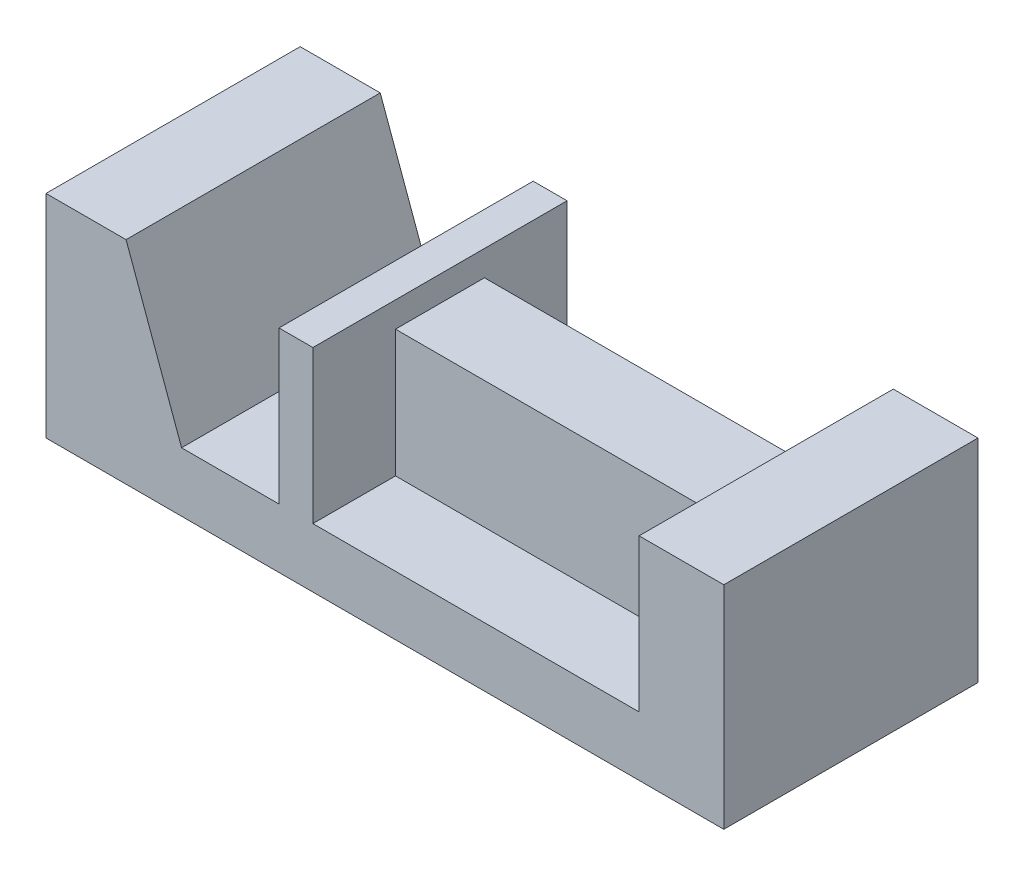
SolidWorks part; units mm, degrees
material "Cast Alloy Steel"
ref_plane "Front Plane" through (0, 0, 0) normal (0, 0, 1) x (1, 0, 0)
ref_plane "Top Plane" through (0, 0, 0) normal (0, 1, 0) x (1, 0, 0)
ref_plane "Right Plane" through (0, 0, 0) normal (1, 0, 0) x (0, 0, -1)
other "Center of Mass"
sketch "Sketch2" plane through (0, 0, 0) normal (0, 0, 1) x (1, 0, 0)
  line L1 (-58.275, 50) -> (101.725, 50)
  line L2 (-58.275, 50) -> (-58.275, 0)
  line L3 (-58.275, 0) -> (101.725, 0)
  line L4 (101.725, 50) -> (101.725, 0)
  dimension "D1" = 160
  dimension "D2" = 50
extrude "Boss-Extrude1" add sketch "Sketch2" along normal blind 60
sketch "Sketch3" plane through (0, 0, 60) normal (0, 0, 1) x (1, 0, 0)
  line L0 (-39.3779, 50) -> (-26.275, 14)
  line L1 (101.725, 50) -> (-58.275, 50) construction
  line L2 (-26.275, 14) -> (-3.275, 14)
  line L3 (-3.275, 14) -> (-3.275, 50)
  line L4 (-3.275, 50) -> (-39.3779, 50)
  line L5 (-39.3779, 50) -> (-39.3779, 0) construction
  line L6 (-58.275, 0) -> (101.725, 0) construction
  dimension "D1" = 23
  dimension "D2" = 20
  dimension "D3" = 14
  dimension "D4" = 55
extrude "Cut-Extrude1" cut sketch "Sketch3" against normal through all
sketch "Sketch4" plane through (0, 0, 60) normal (0, 0, 1) x (1, 0, 0)
  line L0 (4.725, 50) -> (4.725, 14)
  line L1 (101.725, 50) -> (-3.275, 50) construction
  line L2 (4.725, 14) -> (81.725, 14)
  line L3 (81.725, 14) -> (81.725, 50)
  line L4 (81.725, 50) -> (4.725, 50)
  line L5 (-58.275, 0) -> (101.725, 0) construction
  dimension "D1" = 77
  dimension "D2" = 140
  dimension "D3" = 14
extrude "Cut-Extrude3" cut sketch "Sketch4" against normal through all
sketch "Sketch9" plane through (0, 14, 0) normal (0, 1, 0) x (1, 0, 0)
  line L0 (81.725, -30) -> (4.725, -30) construction
  line L1 (81.725, 0) -> (81.725, -60) construction
  line L2 (4.725, 0) -> (4.725, -60) construction
  line L4 (4.725, -19.5) -> (81.725, -19.5)
  line L5 (4.725, -19.5) -> (4.725, -40.5)
  line L6 (4.725, -40.5) -> (81.725, -40.5)
  line L7 (81.725, -19.5) -> (81.725, -40.5)
  line L8 (43.225, -40.5) -> (43.225, -19.5) construction
  line L9 (4.725, -30) -> (81.725, -30) construction
  point P6 (43.225, -30)
  dimension "D1" = 21
extrude "Boss-Extrude4" add sketch "Sketch9" along normal blind 30
